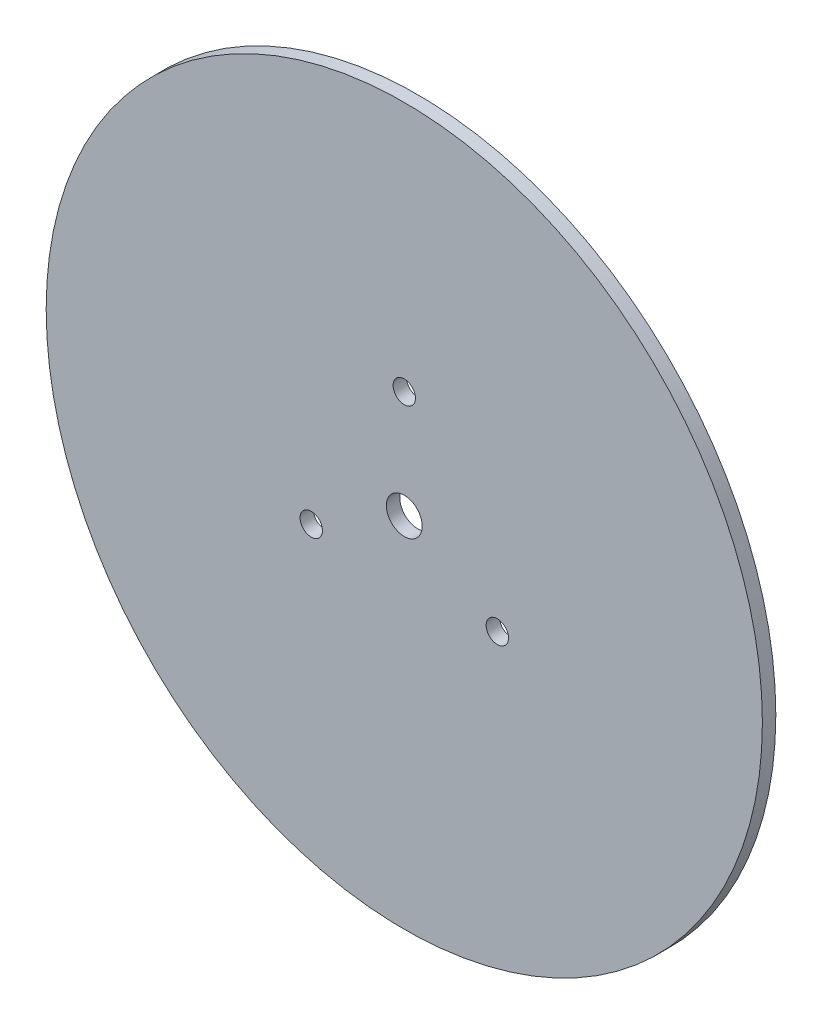
SolidWorks part; units mm, degrees
ref_plane "Front Plane" through (0, 0, 0) normal (0, 0, 1) x (1, 0, 0)
ref_plane "Top Plane" through (0, 0, 0) normal (0, 1, 0) x (1, 0, 0)
ref_plane "Right Plane" through (0, 0, 0) normal (1, 0, 0) x (0, 0, -1)
sketch "Sketch2" plane through (0, 0, 0) normal (0, 0, 1) x (1, 0, 0)
  circle A0 centre (0, 0) radius 80
  circle A1 centre (0, 0) radius 4
  dimension "D1" = 160
  dimension "D2" = 8
extrude "Boss-Extrude1" add sketch "Sketch2" along normal blind 3 contours A0 A1
sketch "Sketch5" plane through (0, 0, 3) normal (0, 0, 1) x (1, 0, 0)
  circle A0 centre (0, 0) radius 24 construction
  circle A1 centre (0, 24) radius 2.5
  circle A2 centre (20.7846, -12) radius 2.5
  circle A3 centre (-20.7846, -12) radius 2.5
  dimension "D1" = 48
  dimension "D2" = 5
  dimension "D3" = 3
extrude "Cut-Extrude1" cut sketch "Sketch5" against normal blind 10
